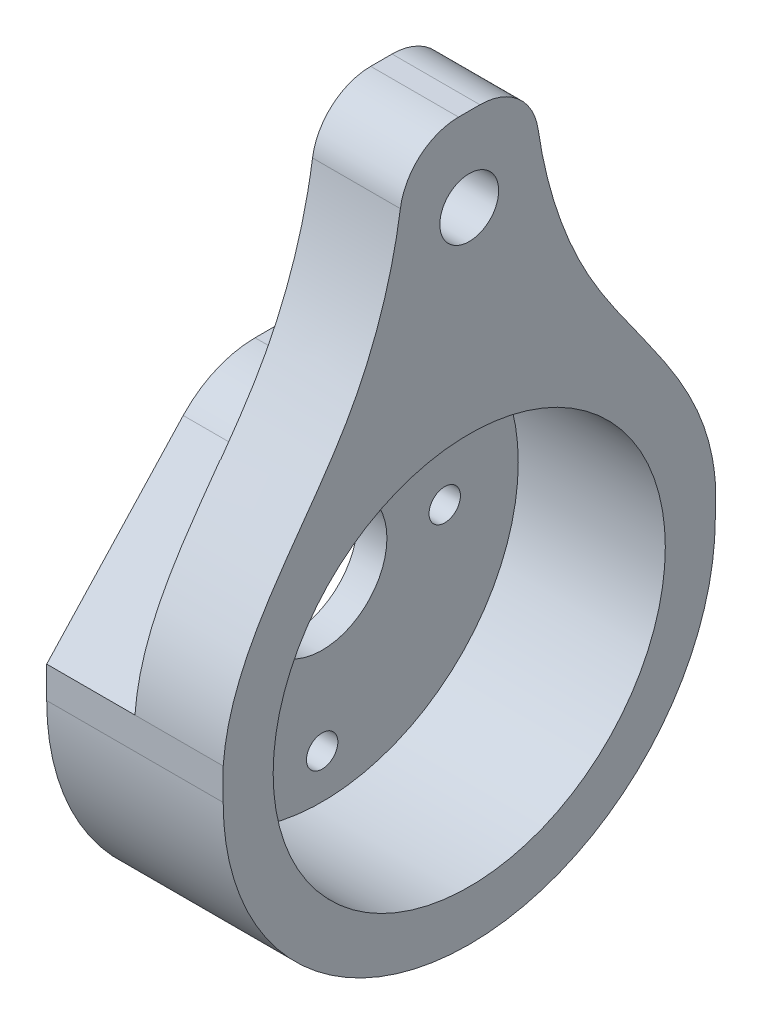
SolidWorks part; units mm, degrees
ref_plane "前视基准面" through (0, 0, 0) normal (0, 0, 1) x (1, 0, 0)
ref_plane "上视基准面" through (0, 0, 0) normal (0, 1, 0) x (1, 0, 0)
ref_plane "右视基准面" through (0, 0, 0) normal (1, 0, 0) x (0, 0, -1)
sketch "Sketch1" plane through (0, 0, 0) normal (1, 0, 0) x (0, 0, -1)
  circle A0 centre (2.9834, 10.8268) radius 7.75 construction
  circle A1 centre (2.9834, 10.8268) radius 6.25 construction
  circle A2 centre (2.9834, 18.5768) radius 0.8
  circle A3 centre (2.9834, 3.0768) radius 0.8
  circle A4 centre (-3.2666, 10.8268) radius 0.8
  circle A5 centre (9.2334, 10.8268) radius 0.8
  circle A6 centre (2.9834, 10.8268) radius 10
  circle A7 centre (2.9834, 10.8268) radius 3.3018
  dimension "D1" = 15.5
  dimension "D2" = 12.5
  dimension "D3" = 20
extrude "Boss-Extrude1" add sketch "Sketch1" along normal blind 1.5
sketch "Sketch2" plane through (0, 0, 0) normal (-1, 0, 0) x (0, 0, 1)
  line L0 (-2.9834, 10.8268) -> (-2.9834, 25.4318) construction
  line L2 (-12.9834, 35.0947) -> (7.0166, 35.0947) construction
  line L3 (-12.9834, 35.0947) -> (-12.9834, 10.8268) construction
  line L4 (-12.9834, 10.8268) -> (7.0166, 10.8268) construction
  line L5 (7.0166, 35.0947) -> (7.0166, 10.8268) construction
  line L6 (-12.9834, 35.0947) -> (7.0166, 10.8268) construction
  line L7 (-12.9834, 10.8268) -> (7.0166, 35.0947) construction
  line L8 (-15.5319, 35.0947) -> (9.5652, 35.0947)
  line L9 (-15.5319, 35.0947) -> (-15.5319, 10.8268)
  line L10 (-15.5319, 10.8268) -> (9.5652, 10.8268) construction
  line L11 (9.5652, 35.0947) -> (9.5652, 10.8268)
  line L12 (-15.5319, 35.0947) -> (9.5652, 10.8268) construction
  line L13 (-15.5319, 10.8268) -> (9.5652, 35.0947) construction
  circle A0 centre (-2.9834, 10.8268) radius 10 construction
  arc A1 (-12.9834, 10.8268) -> (7.0166, 10.8268) centre (-2.9834, 10.8268) cw construction
  circle A2 centre (-2.9834, 10.8268) radius 12.5485 construction
  circle A3 centre (-2.9834, 10.8268) radius 10
  arc A4 (-15.5319, 10.8268) -> (9.5652, 10.8268) centre (-2.9834, 10.8268) ccw
  circle A5 centre (-2.9834, 10.8268) radius 0.6321 construction
  point P1 (-2.9834, 22.9607)
  point P12 (-2.9834, 22.9607)
  dimension "D1" = 0
extrude "Boss-Extrude2" add sketch "Sketch2" against normal blind 9
sketch "Sketch3" plane through (9, 0, 0) normal (1, 0, 0) x (0, 0, -1)
  line L0 (2.9834, 95.8916) -> (2.9834, 22.8694) construction
  line L3 (-0.2543, 36.1504) -> (-0.2543, 97.5726)
  line L4 (-0.2543, 97.5726) -> (-16.389, 97.5726)
  line L5 (-16.389, 97.5726) -> (-16.389, 8.1411)
  line L6 (-16.389, 8.1411) -> (-9.5652, 10.8268)
  line L7 (22.3558, 8.1411) -> (15.5319, 10.8268)
  line L8 (22.3558, 97.5726) -> (22.3558, 8.1411)
  line L9 (6.2211, 97.5726) -> (22.3558, 97.5726)
  line L10 (6.2211, 36.1504) -> (6.2211, 97.5726)
  circle A0 centre (2.9834, 30.8268) radius 1.5
  circle A1 centre (2.9834, 10.8268) radius 1.5125 construction
  spline S0 degree 3 poles (-9.5652, 10.8268) (-9.9968, 16.6219) (-2.4169, 22.9024) (-0.2794, 32.1518) (-0.2543, 36.1504) knots 0 0 0 0 0.563274 1 1 1 1
  spline S1 degree 3 poles (15.5319, 10.8268) (15.9635, 16.6219) (8.3837, 22.9024) (6.2462, 32.1518) (6.2211, 36.1504) knots 0 0 0 0 0.563274 1 1 1 1
  point P21 (-4.3221, 24.4182)
  point P22 (-3.3407, 28.6383)
  point P23 (-7.8062, 17.6955)
  point P24 (-2.6537, 29.2271)
  point P25 (-2.2688, 28.5582)
  point P29 (-2.5984, 27.3495)
  point P30 (-3.1844, 24.6392)
  point P31 (-1.6095, 28.1187)
  dimension "D1" = 20
extrude "Cut-Extrude1" cut sketch "Sketch3" against normal through all both and the other way through all
fillet "Fillet1" radius 3 2 edges at (4.5, 35.0947, -6.2489) (4.5, 35.0947, 0.2821)
sketch "Sketch5" plane through (0, 0, 0) normal (0, 0, 1) x (1, 0, 0)
  line L1 (4.5197, 37.3542) -> (-3.9184, 39.3787)
  line L2 (4.5197, 37.3542) -> (4.5197, 21.5355)
  line L3 (4.5197, 21.5355) -> (-3.9184, 21.5355)
  line L4 (-3.9184, 39.3787) -> (-3.9184, 21.5355)
  point P4 (0, 0)
  point P5 (4.5197, 37.3542)
  point P6 (0, 0)
extrude "Cut-Extrude2" cut sketch "Sketch5" against normal through all both and the other way through all
sketch "Sketch6" plane through (0, 0, 0) normal (-1, 0, 0) x (0, 0, 1)
  line L0 (-15.5319, 12.4364) -> (-7.2372, 21.5355)
  line L1 (5.2226, 21.5355) -> (-11.1894, 21.5355) construction
  line L2 (-7.2372, 21.5355) -> (-16.0452, 21.5355)
  line L3 (-16.0452, 21.5355) -> (-15.5319, 12.4364)
  line L4 (9.5652, 12.4364) -> (1.1203, 21.5355)
  line L5 (1.1203, 21.5355) -> (9.021, 21.9811)
  line L6 (9.021, 21.9811) -> (10.3871, 13.1992)
  line L7 (10.3871, 13.1992) -> (9.5652, 12.4364)
extrude "Cut-Extrude4" cut sketch "Sketch6" against normal blind 4.5
fillet "Fillet4" radius 5 2 edges at (2.25, 21.5355, -7.2372) (2.25, 21.5355, 1.1203)
